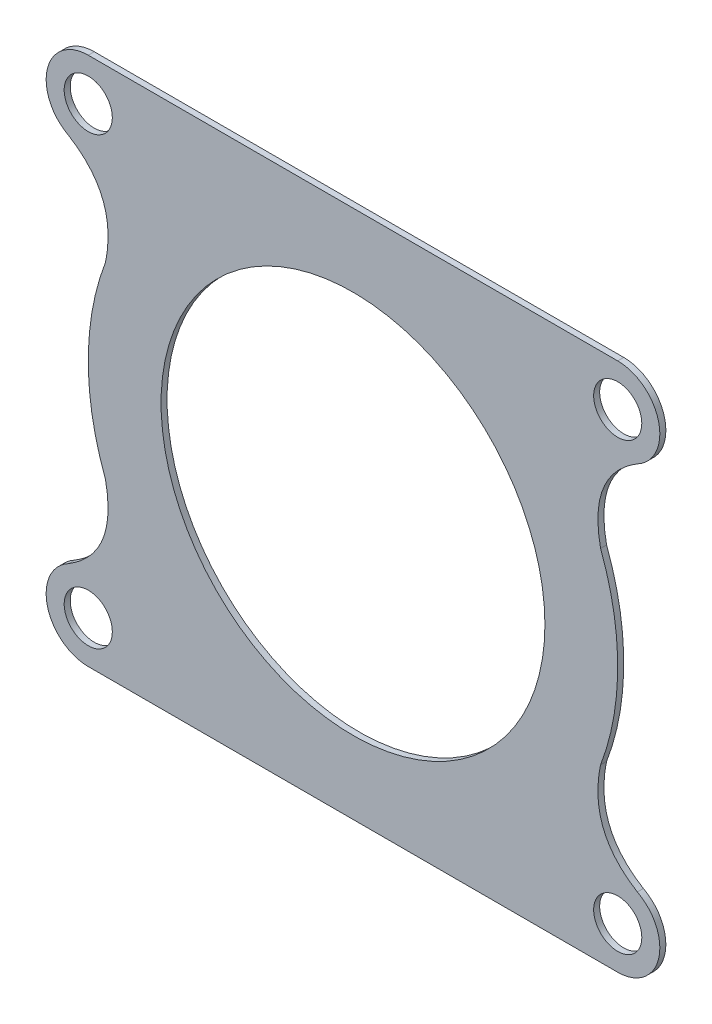
SolidWorks part; units mm, degrees
ref_plane "Front Plane" through (0, 0, 0) normal (0, 0, 1) x (1, 0, 0)
ref_plane "Top Plane" through (0, 0, 0) normal (0, 1, 0) x (1, 0, 0)
ref_plane "Right Plane" through (0, 0, 0) normal (1, 0, 0) x (0, 0, -1)
sketch "Sketch2" plane through (0, 0, 0) normal (0, 0, 1) x (1, 0, 0)
  line L0 (-10.9905, -10.5991) -> (11.0095, -10.5991)
  line L1 (11.0095, 11.4009) -> (-10.9905, 11.4009)
  circle A0 centre (11.0095, 9.6509) radius 1
  circle A1 centre (-10.9905, 9.6509) radius 1
  circle A2 centre (11.0095, -8.8491) radius 1
  arc A3 (-10.9905, 11.4009) -> (-11.806, 8.1025) centre (-10.9905, 9.6509) ccw
  arc A4 (-10.2779, 4.2956) -> (-10.2779, -3.4939) centre (0.0095, 0.4009) ccw
  arc A5 (-11.806, -7.3008) -> (-10.9905, -10.5991) centre (-10.9905, -8.8491) ccw
  arc A6 (11.0095, -10.5991) -> (11.825, -7.3008) centre (11.0095, -8.8491) ccw
  arc A7 (10.2969, -3.4939) -> (10.2969, 4.2956) centre (0.0095, 0.4009) ccw
  arc A8 (11.825, 8.1025) -> (11.0095, 11.4009) centre (11.0095, 9.6509) ccw
  circle A9 centre (-10.9905, -8.8491) radius 1
  circle A10 centre (0.0095, 0.4009) radius 7.975
  parabola Q0 (-11.806, 8.1025) -> (-10.2779, 4.2956) focus (-11.7732, 6.0906) apex (-10.4845, 6.7303)
  parabola Q1 (-10.2779, -3.4939) -> (-11.806, -7.3008) focus (-11.7732, -5.2888) apex (-10.4845, -5.9285)
  parabola Q2 (11.825, -7.3008) -> (10.2969, -3.4939) focus (11.7922, -5.2888) apex (10.5035, -5.9285)
  parabola Q3 (10.2969, 4.2956) -> (11.825, 8.1025) focus (11.7922, 6.0906) apex (10.5035, 6.7303)
extrude "Boss-Extrude1" add sketch "Sketch2" along normal blind 0.25
